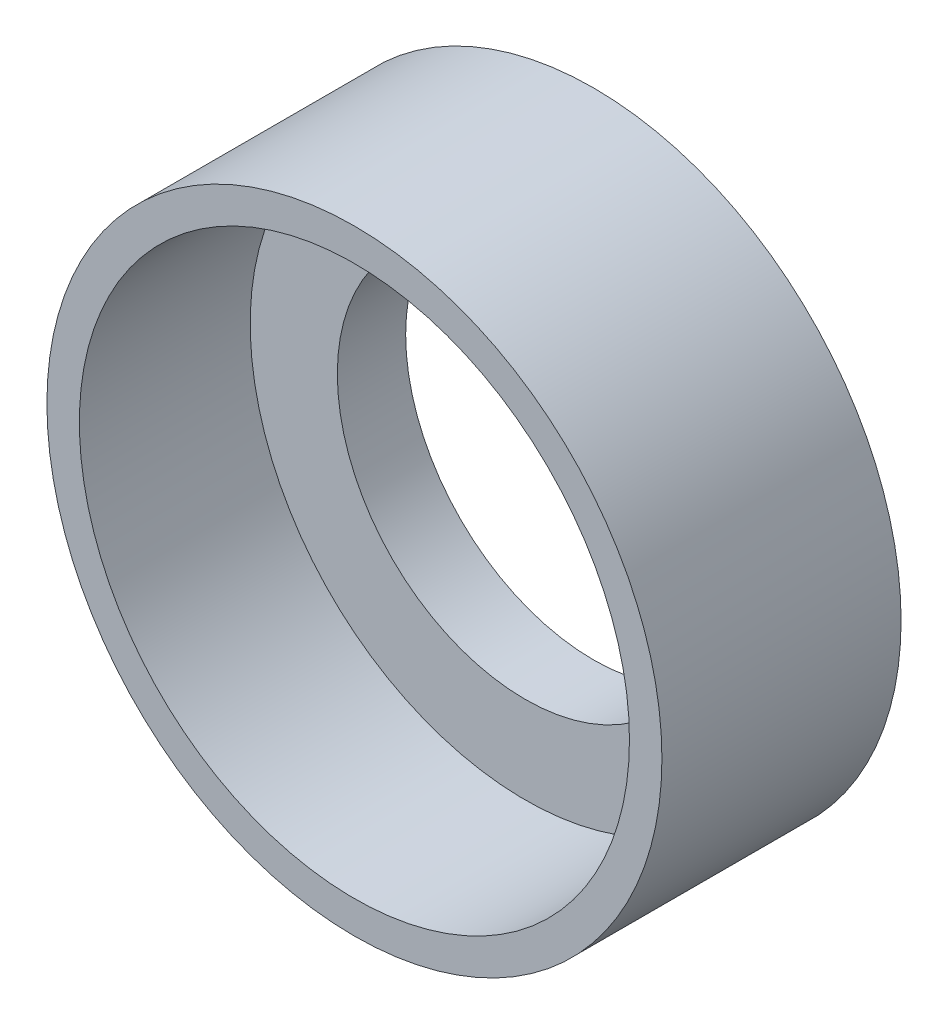
SolidWorks part; units mm, degrees
ref_plane "Front Plane" through (0, 0, 0) normal (0, 0, 1) x (1, 0, 0)
ref_plane "Top Plane" through (0, 0, 0) normal (0, 1, 0) x (1, 0, 0)
ref_plane "Right Plane" through (0, 0, 0) normal (1, 0, 0) x (0, 0, -1)
sketch "Sketch1" plane through (0, 0, 0) normal (0, 0, 1) x (1, 0, 0)
  circle A0 centre (0, 0) radius 9
  circle A1 centre (0, 0) radius 5.5
  dimension "D1" = 18
  dimension "D2" = 11
extrude "Boss-Extrude1" add sketch "Sketch1" along normal blind 2
sketch "Sketch2" plane through (0, 0, 2) normal (0, 0, 1) x (1, 0, 0)
  circle A0 centre (0, 0) radius 9
  circle A1 centre (0, 0) radius 8.05
  dimension "D1" = 18
  dimension "D2" = 16.1
extrude "Boss-Extrude2" add sketch "Sketch2" along normal blind 5
